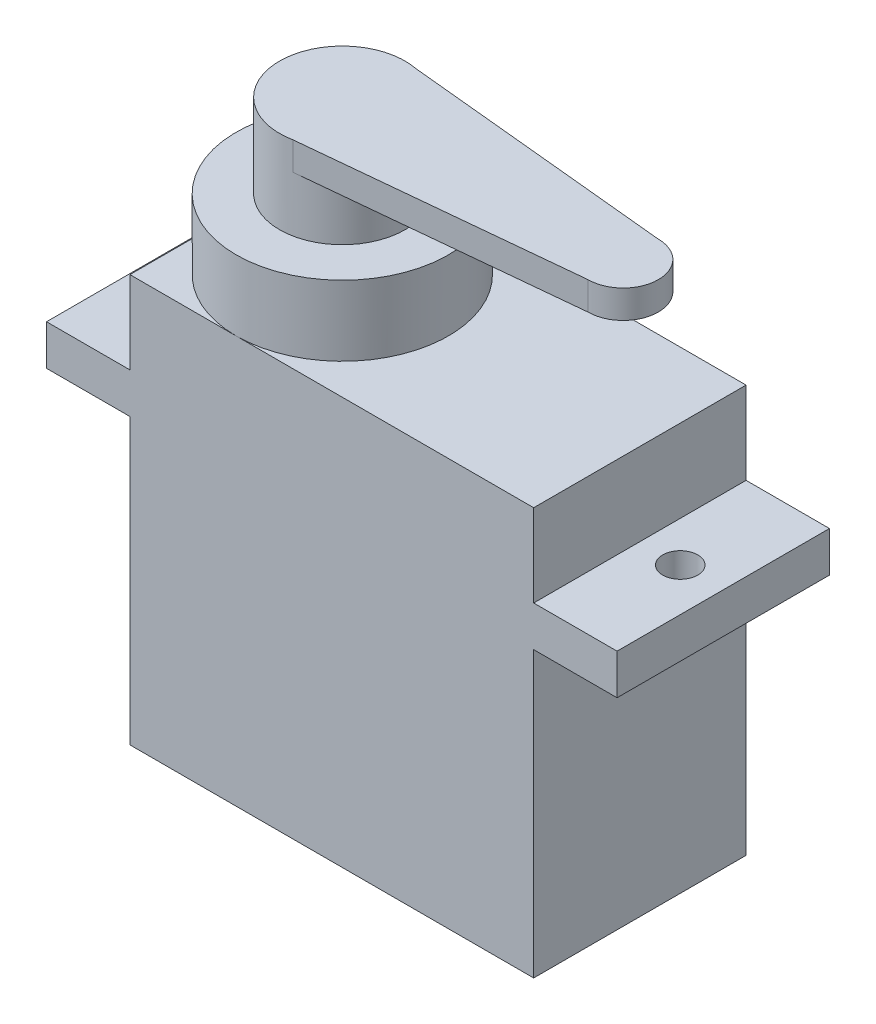
SolidWorks part; units mm, degrees
ref_plane "Front Plane" through (0, 0, 0) normal (0, 0, 1) x (1, 0, 0)
ref_plane "Top Plane" through (0, 0, 0) normal (0, 1, 0) x (1, 0, 0)
ref_plane "Right Plane" through (0, 0, 0) normal (1, 0, 0) x (0, 0, -1)
sketch "Sketch1" plane through (0, 0, 0) normal (0, 1, 0) x (1, 0, 0)
  line L1 (11.5, -6.05) -> (-11.5, -6.05)
  line L2 (11.5, -6.05) -> (11.5, 6.05)
  line L3 (11.5, 6.05) -> (-11.5, 6.05)
  line L4 (-11.5, -6.05) -> (-11.5, 6.05)
  line L5 (11.5, -6.05) -> (-11.5, 6.05) construction
  line L6 (11.5, 6.05) -> (-11.5, -6.05) construction
  point P0 (0, 0)
  dimension "D1" = 12.1
  dimension "D2" = 23
extrude "Boss-Extrude1" add sketch "Sketch1" along normal blind 23.2
sketch "Sketch2" plane through (11.5, 0, 0) normal (1, 0, 0) x (0, 0, -1)
  line L0 (-6.05, 23.2) -> (-6.05, 0) construction
  line L1 (-6.05, 18.5) -> (6.05, 18.5)
  line L2 (-6.05, 18.5) -> (-6.05, 16.2)
  line L3 (-6.05, 16.2) -> (6.05, 16.2)
  line L4 (6.05, 18.5) -> (6.05, 16.2)
  line L5 (6.05, 23.2) -> (6.05, 0) construction
  line L6 (-6.05, 23.2) -> (6.05, 23.2) construction
  dimension "D1" = 2.3
  dimension "D2" = 7
extrude "Boss-Extrude2" add sketch "Sketch2" along normal blind 4.75
sketch "Sketch3" plane through (0, 18.5, 0) normal (0, 1, 0) x (1, 0, 0)
  line L0 (11.5, 0) -> (16.25, 0) construction
  line L1 (11.5, -6.05) -> (11.5, 6.05) construction
  line L2 (16.25, 6.05) -> (16.25, -6.05) construction
  line L3 (13.875, 6.05) -> (13.875, -6.05) construction
  line L4 (16.25, 6.05) -> (11.5, 6.05) construction
  line L5 (16.25, -6.05) -> (11.5, -6.05) construction
  line L6 (11.5, 6.05) -> (11.5, -6.05) construction
  circle A0 centre (13.8, 0) radius 1
  point P16 (0, 0)
  dimension "D1" = 2
  dimension "D2" = 2.3
extrude "Cut-Extrude1" cut sketch "Sketch3" against normal up to surface (2.3 mm away) up to face at (13.875, 16.2, 0)
mirror "Mirror1" about plane through (0, 0, 0) normal (1, 0, 0) of "Cut-Extrude1", "Boss-Extrude2"
sketch "Sketch4" plane through (0, 23.2, 0) normal (0, 1, 0) x (1, 0, 0)
  line L0 (11.5, 6.05) -> (-11.5, 6.05) construction
  line L1 (-11.5, -6.05) -> (11.5, -6.05) construction
  line L2 (-11.5, 6.05) -> (-11.5, -6.05) construction
  circle A0 centre (-5.45, 0) radius 6.05
extrude "Boss-Extrude3" add sketch "Sketch4" along normal blind 4
sketch "Sketch5" plane through (0, 27.2, 0) normal (0, 1, 0) x (1, 0, 0)
  circle A0 centre (-5.45, 0) radius 3.575
  circle A2 centre (-5.45, 0) radius 6.05
  circle A3 centre (-5.45, 0) radius 6.05 construction
  point P2 (-5.45, -0.2022)
  dimension "D2" = 7.15
  dimension "D1" = 0
extrude "Boss-Extrude4" add sketch "Sketch5" along normal blind 4.75
sketch "Sketch7" plane through (0, 31.95, 0) normal (0, 1, 0) x (1, 0, 0)
  line L0 (-5.45, 3.575) -> (10.55, 2)
  line L1 (-5.45, -3.575) -> (10.55, -2)
  line L2 (-5.45, 3.575) -> (-5.45, -3.575)
  circle A2 centre (-5.45, 0) radius 3.575 construction
  circle A3 centre (-5.45, 0) radius 3.575 construction
  arc A5 (10.55, -2) -> (10.55, 2) centre (10.55, 0) ccw
  circle A6 centre (-5.45, 0) radius 3.575
  arc A7 (-5.45, -3.575) -> (-4.7529, -3.5064) centre (-5.45, 0) ccw
  arc A8 (-4.7529, 3.5064) -> (-5.45, 3.575) centre (-5.45, 0) ccw
  point P8 (7.7614, -0.3888)
  point P9 (7.7614, -2.3888)
  point P10 (7.7614, 1.9936)
  point P15 (-4.3629, 3.4057)
  point P16 (7.3866, 2)
  circle M7 centre (-5.45, 0) radius 3.575
  dimension "D2" = 4
  dimension "D3" = 16
  dimension "D1" = 0
extrude "Boss-Extrude5" add sketch "Sketch7" against normal blind 1.6 contours L1 A5 L0 M7
